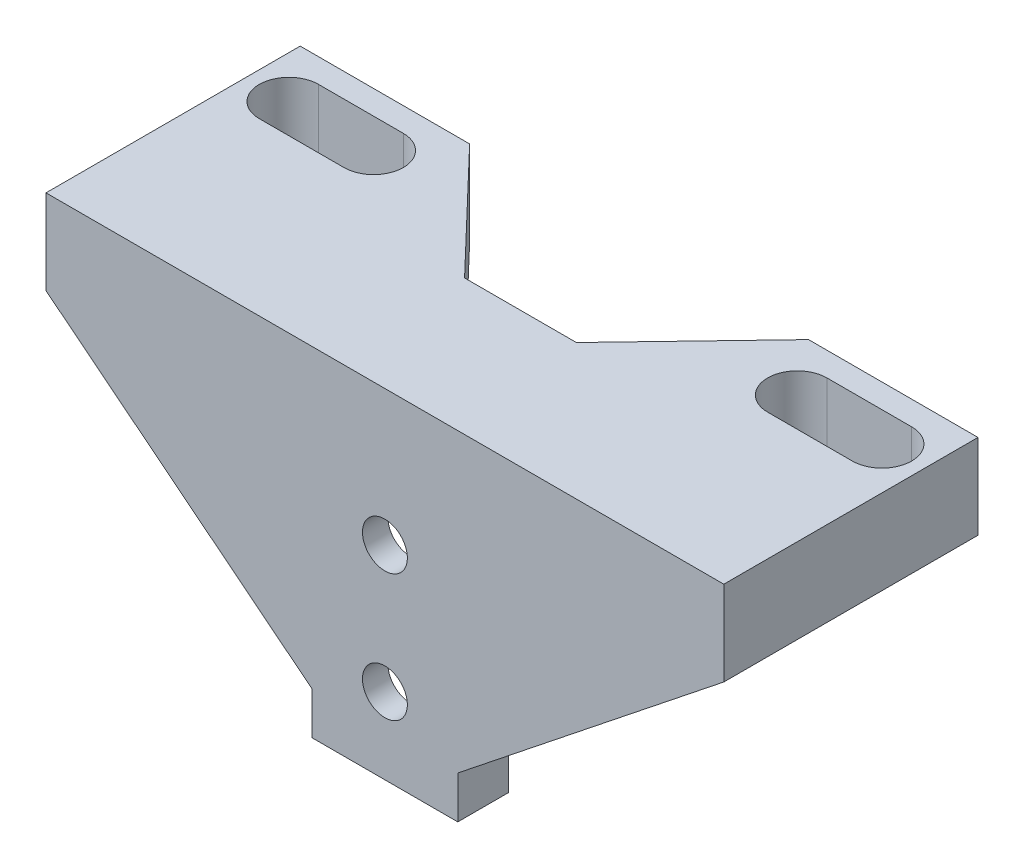
SolidWorks part; units mm, degrees
ref_plane "Plan de face" through (0, 0, 0) normal (0, 0, 1) x (1, 0, 0)
ref_plane "Plan de dessus" through (0, 0, 0) normal (0, 1, 0) x (1, 0, 0)
ref_plane "Plan de droite" through (0, 0, 0) normal (1, 0, 0) x (0, 0, -1)
sketch "Esquisse1" plane through (0, 0, 0) normal (0, 0, 1) x (1, 0, 0)
  line L1 (-7.0379, 12.6832) -> (6.1621, 12.6832)
  line L2 (-7.0379, 12.6832) -> (-7.0379, -17.3168)
  line L3 (-7.0379, -17.3168) -> (6.1621, -17.3168)
  line L4 (6.1621, 12.6832) -> (6.1621, -17.3168)
  line L5 (-7.0379, 12.6832) -> (-9.0379, 12.6832)
  line L6 (-7.0379, 12.6832) -> (-7.0379, -17.3168)
  line L7 (-7.0379, -17.3168) -> (-9.0379, -17.3168)
  line L8 (-9.0379, 12.6832) -> (-9.0379, -17.3168)
  line L9 (6.1621, 12.6832) -> (8.1621, 12.6832)
  line L10 (6.1621, 12.6832) -> (6.1621, -17.3168)
  line L11 (6.1621, -17.3168) -> (8.1621, -17.3168)
  line L12 (8.1621, 12.6832) -> (8.1621, -17.3168)
  dimension "D1" = 30
  dimension "D2" = 13.2
  dimension "D3" = 2
extrude "Boss.-Extru.1" add sketch "Esquisse1" along normal blind 3 contours L4 L1 L2 L3 | L5 L8 L7 L2 | L12 L9 L4 L11
sketch "Esquisse2" plane through (0, 0, 0) normal (0, 0, -1) x (-1, 0, 0)
  line L0 (7.0379, -17.3168) -> (-6.1621, -17.3168) construction
  line L1 (-6.1621, 12.6832) -> (-6.1621, -17.3168) construction
  line L2 (-6.1621, 12.6832) -> (-6.1621, -17.3168) construction
  line L3 (-6.1621, 12.6832) -> (-8.1621, 12.6832) construction
  line L4 (-8.1621, -17.3168) -> (9.0379, -17.3168)
  line L5 (9.0379, -17.3168) -> (9.0379, 12.6832)
  line L6 (9.0379, 12.6832) -> (-8.1621, 12.6832)
  line L7 (-8.1621, 12.6832) -> (-8.1621, -17.3168)
  line L8 (-8.1621, -17.3168) -> (9.0379, -17.3168)
  line L9 (9.0379, -17.3168) -> (9.0379, 12.6832)
  line L10 (9.0379, 12.6832) -> (-8.1621, 12.6832)
  line L11 (-8.1621, 12.6832) -> (-8.1621, -17.3168)
  line L12 (-8.1621, 12.6832) -> (-8.1621, -17.3168) construction
  line L13 (-6.1621, -17.3168) -> (-8.1621, -17.3168) construction
  line L14 (7.0379, 12.6832) -> (7.0379, -17.3168) construction
  line L15 (7.0379, 12.6832) -> (7.0379, -17.3168) construction
  line L16 (7.0379, 12.6832) -> (9.0379, 12.6832) construction
  line L17 (9.0379, 12.6832) -> (9.0379, -17.3168) construction
  line L18 (7.0379, -17.3168) -> (9.0379, -17.3168) construction
  line L19 (7.0379, 12.6832) -> (-6.1621, 12.6832) construction
  line L20 (7.0379, -17.3168) -> (-6.1621, -17.3168)
  line L21 (-6.1621, 12.6832) -> (-6.1621, -17.3168)
  line L22 (-6.1621, 12.6832) -> (-6.1621, -17.3168)
  line L23 (-6.1621, 12.6832) -> (-8.1621, 12.6832)
  line L24 (-8.1621, 12.6832) -> (-8.1621, -17.3168)
  line L25 (-6.1621, -17.3168) -> (-8.1621, -17.3168)
  line L26 (7.0379, 12.6832) -> (7.0379, -17.3168)
  line L27 (7.0379, 12.6832) -> (7.0379, -17.3168)
  line L28 (7.0379, 12.6832) -> (9.0379, 12.6832)
  line L29 (9.0379, 12.6832) -> (9.0379, -17.3168)
  line L30 (7.0379, -17.3168) -> (9.0379, -17.3168)
  line L31 (7.0379, 12.6832) -> (-6.1621, 12.6832)
  line M5 (-8.1621, -17.3168) -> (9.0379, -17.3168)
  line M6 (9.0379, -17.3168) -> (9.0379, 12.6832)
  line M7 (9.0379, 12.6832) -> (-8.1621, 12.6832)
  line M8 (-8.1621, 12.6832) -> (-8.1621, -17.3168)
  dimension "D1" = 0
extrude "Boss.-Extru.2" add sketch "Esquisse2" along normal blind 3 contours L21 L10 M8 M5 | L26 M7 M5 M6
sketch "Esquisse3" plane through (0, 12.6832, 0) normal (0, 1, 0) x (1, 0, 0)
  line L0 (-0.4379, 3) -> (-0.4379, -3) construction
  line L1 (8.1621, -3) -> (-9.0379, -3)
  line L2 (8.1621, -3) -> (8.1621, 3)
  line L3 (8.1621, 3) -> (-9.0379, 3)
  line L4 (-9.0379, -3) -> (-9.0379, 3)
  line L5 (-9.0379, 3) -> (-40.4379, 3)
  line L6 (-9.0379, 3) -> (-9.0379, -3)
  line L7 (-9.0379, -3) -> (-40.4379, -3)
  line L8 (6.1621, 0) -> (-7.0379, 0)
  line L9 (-7.0379, 0) -> (-7.0379, 3)
  line L10 (-7.0379, 3) -> (-9.0379, 3)
  line L11 (-9.0379, 3) -> (-9.0379, -3)
  line L12 (-9.0379, -3) -> (8.1621, -3)
  line L13 (8.1621, -3) -> (8.1621, 3)
  line L14 (8.1621, 3) -> (6.1621, 3)
  line L15 (6.1621, 3) -> (6.1621, 0)
  line L16 (6.1621, 0) -> (-7.0379, 0)
  line L17 (-7.0379, 0) -> (-7.0379, 3)
  line L18 (-7.0379, 3) -> (-9.0379, 3)
  line L19 (-9.0379, 3) -> (-9.0379, -3)
  line L20 (-9.0379, -3) -> (8.1621, -3)
  line L21 (8.1621, -3) -> (8.1621, 3)
  line L22 (8.1621, 3) -> (6.1621, 3)
  line L23 (6.1621, 3) -> (6.1621, 0)
  line L24 (-40.4379, 3) -> (-40.4379, -3)
  line L25 (8.1621, -3) -> (39.5621, -3)
  line L26 (-40.4379, -3) -> (-20.4379, -3)
  line L27 (-40.4379, -3) -> (-40.4379, 27)
  line L28 (-40.4379, 27) -> (-20.4379, 27)
  line L29 (-20.4379, -3) -> (-20.4379, 27)
  line L30 (39.5621, 3) -> (39.5621, -3)
  line L31 (8.1621, 3) -> (39.5621, 3)
  line L32 (8.1621, 3) -> (8.1621, -3)
  line L33 (39.5621, 27) -> (19.5621, 27)
  line L34 (19.5621, -3) -> (19.5621, 27)
  line L35 (39.5621, -3) -> (19.5621, -3)
  line L36 (39.5621, -3) -> (39.5621, 27)
  line L37 (-20.4379, 27) -> (-7.0379, 13)
  line L38 (6.1621, 13) -> (19.5621, 27)
  line L40 (-7.0379, 0) -> (6.1621, 0)
  line L41 (-7.0379, 0) -> (-7.0379, 13)
  line L42 (-7.0379, 13) -> (6.1621, 13)
  line L43 (6.1621, 0) -> (6.1621, 13)
  dimension "D2" = 40
  dimension "D3" = 20
  dimension "D4" = 30
  dimension "D5" = 13
  dimension "D1" = 0
extrude "Boss.-Extru.3" add sketch "Esquisse3" along normal blind 10
sketch "Esquisse5" plane through (0, 0, 3) normal (0, 0, 1) x (1, 0, 0)
  line L0 (-40.4379, 12.6832) -> (-9.0379, -12.3168)
  line L1 (-0.4379, -17.3168) -> (-0.4379, 22.6832) construction
  line L2 (39.5621, 12.6832) -> (8.1621, -12.3168)
  line L8 (-9.0379, -17.3168) -> (8.1621, -17.3168)
  line L9 (8.1621, -17.3168) -> (8.1621, 12.6832)
  line L10 (8.1621, 12.6832) -> (39.5621, 12.6832)
  line L11 (39.5621, 12.6832) -> (39.5621, 22.6832)
  line L12 (39.5621, 22.6832) -> (-40.4379, 22.6832)
  line L13 (-40.4379, 22.6832) -> (-40.4379, 12.6832)
  line L14 (-40.4379, 12.6832) -> (-9.0379, 12.6832)
  line L15 (-9.0379, 12.6832) -> (-9.0379, -17.3168)
  line L16 (-9.0379, -17.3168) -> (8.1621, -17.3168)
  line L17 (8.1621, -17.3168) -> (8.1621, 12.6832)
  line L18 (8.1621, 12.6832) -> (39.5621, 12.6832)
  line L19 (39.5621, 12.6832) -> (39.5621, 22.6832)
  line L20 (39.5621, 22.6832) -> (-40.4379, 22.6832)
  line L21 (-40.4379, 22.6832) -> (-40.4379, 12.6832)
  line L22 (-40.4379, 12.6832) -> (-9.0379, 12.6832)
  line L23 (-9.0379, 12.6832) -> (-9.0379, -17.3168)
  line M12 (8.1621, -17.3168) -> (8.1621, 12.6832)
  line M13 (8.1621, 12.6832) -> (39.5621, 12.6832)
  line M17 (-40.4379, 12.6832) -> (-9.0379, 12.6832)
  line M18 (-9.0379, 12.6832) -> (-9.0379, -17.3168)
  dimension "D2" = 5
  dimension "D1" = 0
extrude "Boss.-Extru.4" add sketch "Esquisse5" against normal up to surface (6 mm away) contours L0 M17 M18 | L2 M13 M12 up to face at (7.1621, -2.3168, -3)
sketch "Esquisse6" plane through (0, 0, 0) normal (0, 0, -1) x (-1, 0, 0)
  line L0 (0.4379, 12.6832) -> (0.4379, -17.3168) construction
  line L4 (7.0379, -17.3168) -> (7.0379, 12.6832)
  line L5 (7.0379, 12.6832) -> (-6.1621, 12.6832)
  line L6 (-6.1621, 12.6832) -> (-6.1621, -17.3168)
  line L7 (-6.1621, -17.3168) -> (7.0379, -17.3168)
  line L8 (7.0379, -17.3168) -> (7.0379, 12.6832)
  line L9 (7.0379, 12.6832) -> (-6.1621, 12.6832)
  line L10 (-6.1621, 12.6832) -> (-6.1621, -17.3168)
  line L11 (-6.1621, -17.3168) -> (7.0379, -17.3168)
  circle A0 centre (0.4379, 6.6832) radius 2.65
  circle A1 centre (0.4379, -8.3168) radius 2.65
  dimension "D3" = 5.3
  dimension "D5" = 5.3
  dimension "D2" = 6
  dimension "D4" = 15
  dimension "D1" = 0
extrude "Enlèv. mat.-Extru.1" cut sketch "Esquisse6" against normal through all contours A1 L0 | A0
sketch "Esquisse7" plane through (0, 22.6832, 0) normal (0, 1, 0) x (1, 0, 0)
  line L0 (-0.4379, -3) -> (-0.4379, 3) construction
  line L1 (-40.4379, 20.6692) -> (39.5621, 20.6692) construction
  line L2 (-40.4379, 20.6692) -> (-30.1879, 20.6692)
  line L3 (29.3121, 20.6692) -> (39.5621, 20.6692)
  line L4 (-25.4379, 20.6692) -> (-35.4379, 20.6692) construction
  line L5 (-25.4379, 17.1692) -> (-35.4379, 17.1692)
  line L6 (-25.4379, 24.1692) -> (-35.4379, 24.1692)
  line L7 (34.5621, 20.6692) -> (24.5621, 20.6692) construction
  line L8 (19.5621, 27) -> (6.1621, 13)
  line L10 (-20.4379, 27) -> (-40.4379, 27)
  line L11 (-40.4379, 27) -> (-40.4379, -3)
  line L12 (-40.4379, -3) -> (39.5621, -3)
  line L13 (39.5621, -3) -> (39.5621, 27)
  line L14 (39.5621, 27) -> (19.5621, 27)
  line L15 (19.5621, 27) -> (6.1621, 13)
  line L18 (-20.4379, 27) -> (-40.4379, 27)
  line L19 (-40.4379, 27) -> (-40.4379, -3)
  line L20 (-40.4379, -3) -> (39.5621, -3)
  line L21 (39.5621, -3) -> (39.5621, 27)
  line L22 (39.5621, 27) -> (19.5621, 27)
  line L24 (34.5621, 17.1692) -> (24.5621, 17.1692)
  line L25 (34.5621, 24.1692) -> (24.5621, 24.1692)
  line L35 (6.1621, 13) -> (-7.0379, 13)
  line L36 (6.1621, 13) -> (-7.0379, 13)
  line L43 (-7.0379, 13) -> (-20.4379, 27)
  line L44 (-7.0379, 13) -> (-20.4379, 27)
  arc A2 (-25.4379, 17.1692) -> (-25.4379, 24.1692) centre (-25.4379, 20.6692) ccw
  arc A3 (-35.4379, 24.1692) -> (-35.4379, 17.1692) centre (-35.4379, 20.6692) ccw
  arc A4 (34.5621, 17.1692) -> (34.5621, 24.1692) centre (34.5621, 20.6692) ccw
  arc A5 (24.5621, 24.1692) -> (24.5621, 17.1692) centre (24.5621, 20.6692) ccw
  point P10 (-30.1879, 20.6692)
  point P12 (29.3121, 20.6692)
  point P18 (-30.4379, 20.6692)
  point P23 (29.5621, 20.6692)
  dimension "D4" = 3.5
  dimension "D5" = 3.5
  dimension "D2" = 80
  dimension "D3" = 59.5
  dimension "D6" = 5
  dimension "D9" = 5
  dimension "D1" = 0
extrude "Enlèv. mat.-Extru.2" cut sketch "Esquisse7" against normal through all
chamfer "Chanfrein2" distance 10 angle 45 2 edges at (-23.7379, 12.6832, -3) (22.8621, 12.6832, -3)
